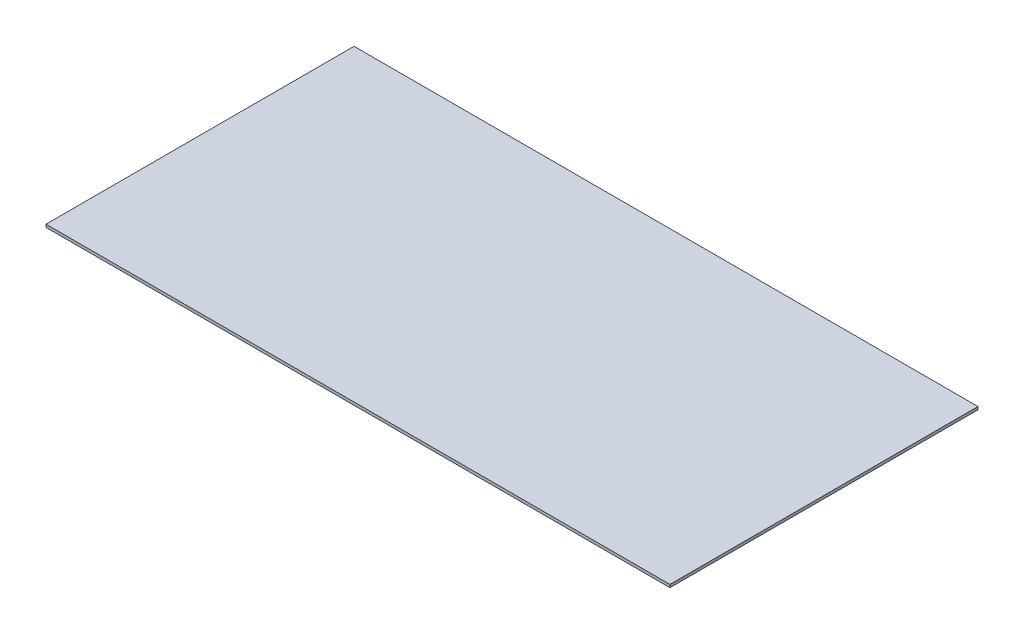
SolidWorks part; units mm, degrees
material "Oak"
ref_plane "Front Plane" through (0, 0, 0) normal (0, 0, 1) x (1, 0, 0)
ref_plane "Top Plane" through (0, 0, 0) normal (0, 1, 0) x (1, 0, 0)
ref_plane "Right Plane" through (0, 0, 0) normal (1, 0, 0) x (0, 0, -1)
sketch "Sketch1" plane through (0, 0, 0) normal (0, 1, 0) x (1, 0, 0)
  line L1 (-609.6, -300.99) -> (609.6, -300.99)
  line L2 (-609.6, -300.99) -> (-609.6, 300.99)
  line L3 (-609.6, 300.99) -> (609.6, 300.99)
  line L4 (609.6, -300.99) -> (609.6, 300.99)
  line L5 (-609.6, -300.99) -> (609.6, 300.99) construction
  line L6 (-609.6, 300.99) -> (609.6, -300.99) construction
  point P0 (0, 0)
  dimension "D1" = 1219.2
  dimension "D2" = 601.98
extrude "Boss-Extrude1" add sketch "Sketch1" along normal blind 5.5562
